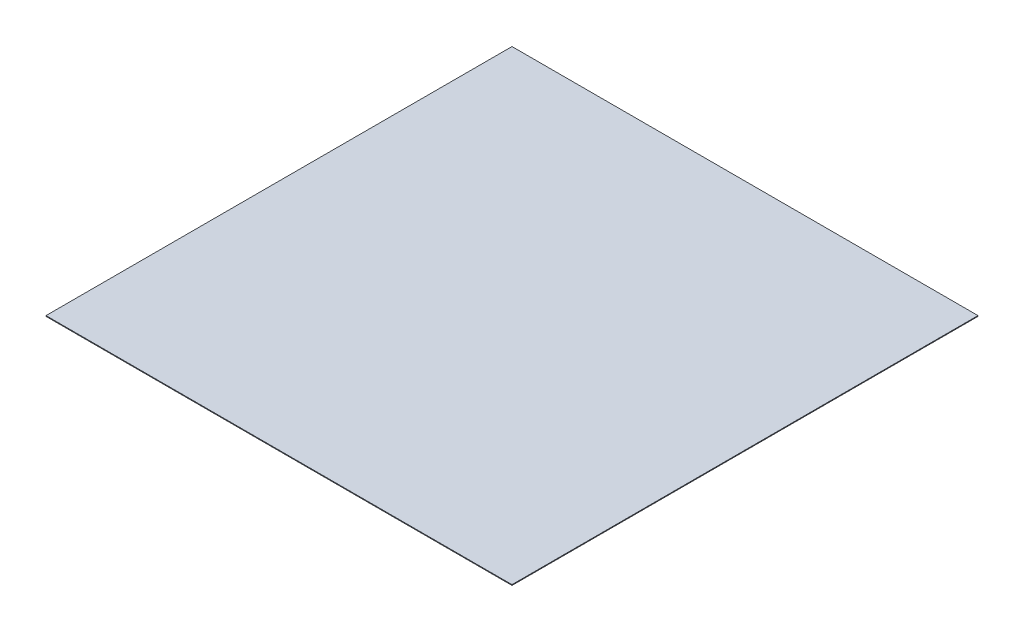
SolidWorks part; units mm, degrees
ref_plane "前视基准面" through (0, 0, 0) normal (0, 0, 1) x (1, 0, 0)
ref_plane "上视基准面" through (0, 0, 0) normal (0, 1, 0) x (1, 0, 0)
ref_plane "右视基准面" through (0, 0, 0) normal (1, 0, 0) x (0, 0, -1)
sketch "草图1" plane through (0, 0, 0) normal (0, 1, 0) x (1, 0, 0)
  line L1 (0, 0) -> (320, 0)
  line L2 (0, 0) -> (0, 320)
  line L3 (0, 320) -> (320, 320)
  line L4 (320, 0) -> (320, 320)
  dimension "D1" = 320
extrude "凸台-拉伸1" add sketch "草图1" along normal blind 0.5
